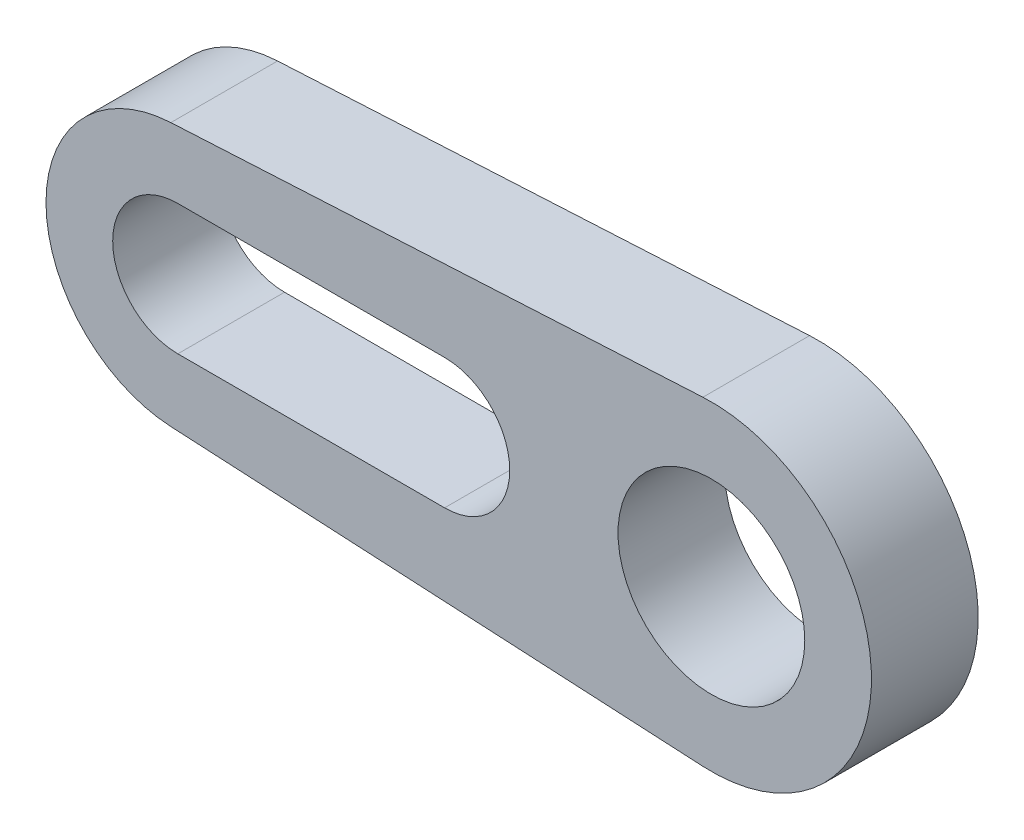
SolidWorks part; units mm, degrees
ref_plane "Front" through (0, 0, 0) normal (0, 0, 1) x (1, 0, 0)
ref_plane "Top" through (0, 0, 0) normal (0, 1, 0) x (1, 0, 0)
ref_plane "Right" through (0, 0, 0) normal (1, 0, 0) x (0, 0, -1)
sketch "Sketch1" plane through (0, 0, 0) normal (0, 0, 1) x (1, 0, 0)
  line L0 (-12.8661, 3.1331) -> (-0.2017, 3.8047)
  line L1 (-12.8661, -3.1331) -> (-0.2017, -3.8047)
  line L2 (-6.35, 1.55) -> (-12.7, 1.55)
  line L3 (-12.7, -1.55) -> (-6.35, -1.55)
  circle A0 centre (0, 0) radius 3.81
  circle A1 centre (-12.7, 0) radius 3.1375
  circle A2 centre (-12.7, 0) radius 1.55
  circle A3 centre (0, 0) radius 2.2225
  circle A4 centre (-6.35, 0) radius 1.55
  dimension "D1" = 3.1
  dimension "D2" = 1.5875
  dimension "D3" = 1.5875
  dimension "D5" = 7.62
  dimension "D4" = 12.7
  dimension "D6" = 6.35
extrude "Boss-Extrude1" add sketch "Sketch1" along normal blind 2.54 contours A4 L3 A1 L1 A0 L0 L2 | A0 A3 | A2 | A2 L3 A1 L2
